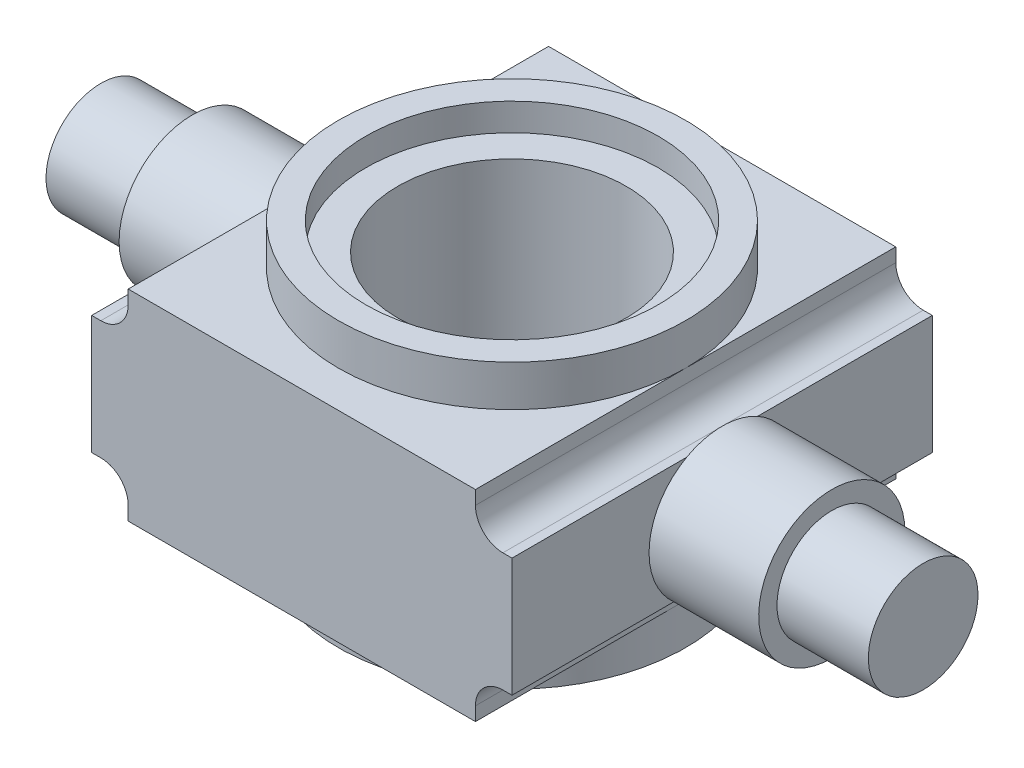
SolidWorks part; units mm, degrees
ref_plane "Front Plane" through (0, 0, 0) normal (0, 0, 1) x (1, 0, 0)
ref_plane "Top Plane" through (0, 0, 0) normal (0, 1, 0) x (1, 0, 0)
ref_plane "Right Plane" through (0, 0, 0) normal (1, 0, 0) x (0, 0, -1)
sketch "Sketch1" plane through (0, 0, 0) normal (0, 1, 0) x (1, 0, 0)
  line L1 (-23, 23) -> (23, 23)
  line L2 (-23, 23) -> (-23, -23)
  line L3 (-23, -23) -> (23, -23)
  line L4 (23, 23) -> (23, -23)
  line L5 (-23, 23) -> (23, -23) construction
  line L6 (-23, -23) -> (23, 23) construction
  point P0 (0, 0)
  dimension "D1" = 46
  dimension "D2" = 46
extrude "Boss-Extrude1" add sketch "Sketch1" along normal blind 22
sketch "Sketch2" plane through (0, 22, 0) normal (0, 1, 0) x (1, 0, 0)
  circle A0 centre (0, 0) radius 19
  dimension "D1" = 38
extrude "Boss-Extrude4" add sketch "Sketch2" along normal blind 4.5
sketch "Sketch5" plane through (0, 0, 0) normal (0, -1, 0) x (1, 0, 0)
  circle A0 centre (0, 0) radius 19
  dimension "D1" = 38
extrude "Boss-Extrude5" add sketch "Sketch5" along normal blind 4.5
sketch "Sketch6" plane through (0, 26.5, 0) normal (0, 1, 0) x (1, 0, 0)
  circle A0 centre (0, 0) radius 16
  dimension "D1" = 32
extrude "Cut-Extrude1" cut sketch "Sketch6" against normal blind 3
sketch "Sketch7" plane through (0, 23.5, 0) normal (0, 1, 0) x (1, 0, 0)
  circle A0 centre (0, 0) radius 12.5
  dimension "D1" = 25
extrude "Cut-Extrude2" cut sketch "Sketch7" against normal through all
sketch "Sketch8" plane through (23, 0, 0) normal (1, 0, 0) x (0, 0, -1)
  line L0 (0, -8.232) -> (0, 29.2434) construction
  circle A0 centre (0, 10.5057) radius 8
  point P6 (0, 10.5057)
  dimension "D1" = 16
extrude "Boss-Extrude6" add sketch "Sketch8" along normal blind 12
sketch "Sketch9" plane through (35, 0, 0) normal (1, 0, 0) x (0, 0, -1)
  circle A0 centre (0, 10.5057) radius 6
  dimension "D1" = 12
extrude "Boss-Extrude7" add sketch "Sketch9" along normal blind 10
sketch "Sketch10" plane through (-23, 0, 0) normal (-1, 0, 0) x (0, 0, 1)
  line L0 (0, 0) -> (0, 22) construction
  line L1 (-23, 22) -> (23, 22) construction
  circle A0 centre (0, 11) radius 8
  dimension "D1" = 16
extrude "Boss-Extrude8" add sketch "Sketch10" along normal blind 12
sketch "Sketch11" plane through (-35, 0, 0) normal (-1, 0, 0) x (0, 0, 1)
  circle A0 centre (0, 11) radius 6
  dimension "D1" = 12
extrude "Boss-Extrude9" add sketch "Sketch11" along normal blind 10
sketch "Sketch13" plane through (0, 0, 23) normal (0, 0, 1) x (1, 0, 0)
  line L0 (-23, 22) -> (-19, 22)
  line L1 (-19, 22) -> (-19, 20.5)
  line L2 (-22, 17.5) -> (-23, 17.5)
  line L3 (-23, 22) -> (-23, 0) construction
  line L4 (-23, 17.5) -> (-23, 22)
  line L5 (23, 22) -> (19, 22)
  line L6 (-23, 22) -> (23, 22) construction
  line L7 (19, 22) -> (19, 20.5)
  line L8 (22, 17.5) -> (23, 17.5)
  line L9 (23, 22) -> (23, 0) construction
  line L10 (23, 17.5) -> (23, 22)
  line L11 (-23, 0) -> (-19, 0)
  line L12 (-23, 0) -> (23, 0) construction
  line L13 (-19, 0) -> (-19, 1.5)
  line L14 (-22, 4.5) -> (-23, 4.5)
  line L15 (-23, 19) -> (-23, 3) construction
  line L16 (-23, 4.5) -> (-23, 0)
  line L17 (23, 0) -> (23, 4.5)
  line L18 (23, 4.5) -> (22, 4.5)
  line L19 (19, 1.5) -> (19, 0)
  line L20 (19, 0) -> (23, 0)
  arc A0 (-22, 17.5) -> (-19, 20.5) centre (-22, 20.5) ccw
  arc A1 (22, 17.5) -> (19, 20.5) centre (22, 20.5) cw
  arc A2 (-19, 1.5) -> (-22, 4.5) centre (-22, 1.5) ccw
  arc A3 (19, 1.5) -> (22, 4.5) centre (22, 1.5) cw
  dimension "D1" = 3
  dimension "D2" = 3
  dimension "D3" = 3
  dimension "D4" = 3
extrude "Cut-Extrude3" cut sketch "Sketch13" against normal through all
